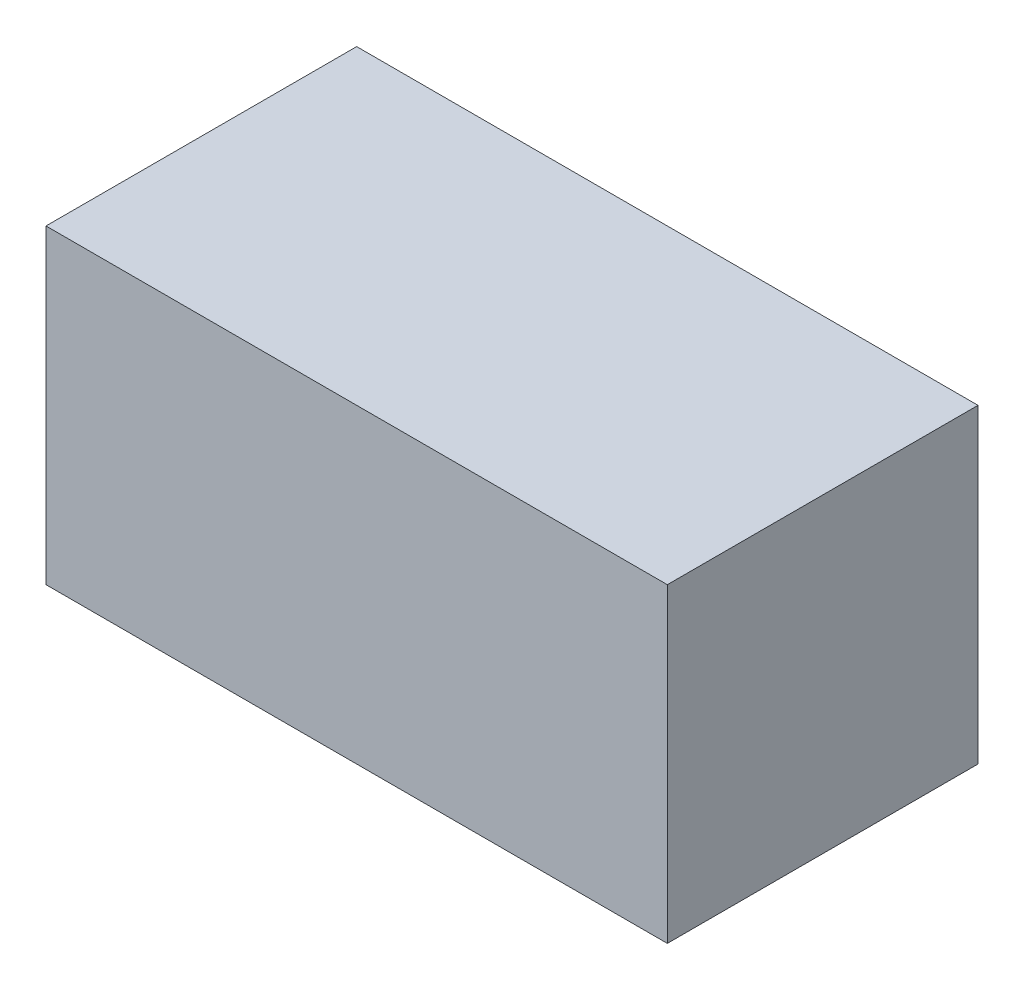
SolidWorks part; units mm, degrees
ref_plane "Front Plane" through (0, 0, 0) normal (0, 0, 1) x (1, 0, 0)
ref_plane "Top Plane" through (0, 0, 0) normal (0, 1, 0) x (1, 0, 0)
ref_plane "Right Plane" through (0, 0, 0) normal (1, 0, 0) x (0, 0, -1)
sketch "Sketch2" plane through (0, 0, 0) normal (0, 1, 0) x (1, 0, 0)
  line L1 (-15, 7.5) -> (15, 7.5)
  line L2 (-15, 7.5) -> (-15, -7.5)
  line L3 (-15, -7.5) -> (15, -7.5)
  line L4 (15, 7.5) -> (15, -7.5)
  line L5 (-15, 7.5) -> (15, -7.5) construction
  line L6 (-15, -7.5) -> (15, 7.5) construction
  point P0 (0, 0)
  dimension "D1" = 30
  dimension "D2" = 15
extrude "Boss-Extrude1" add sketch "Sketch2" along normal blind 15
